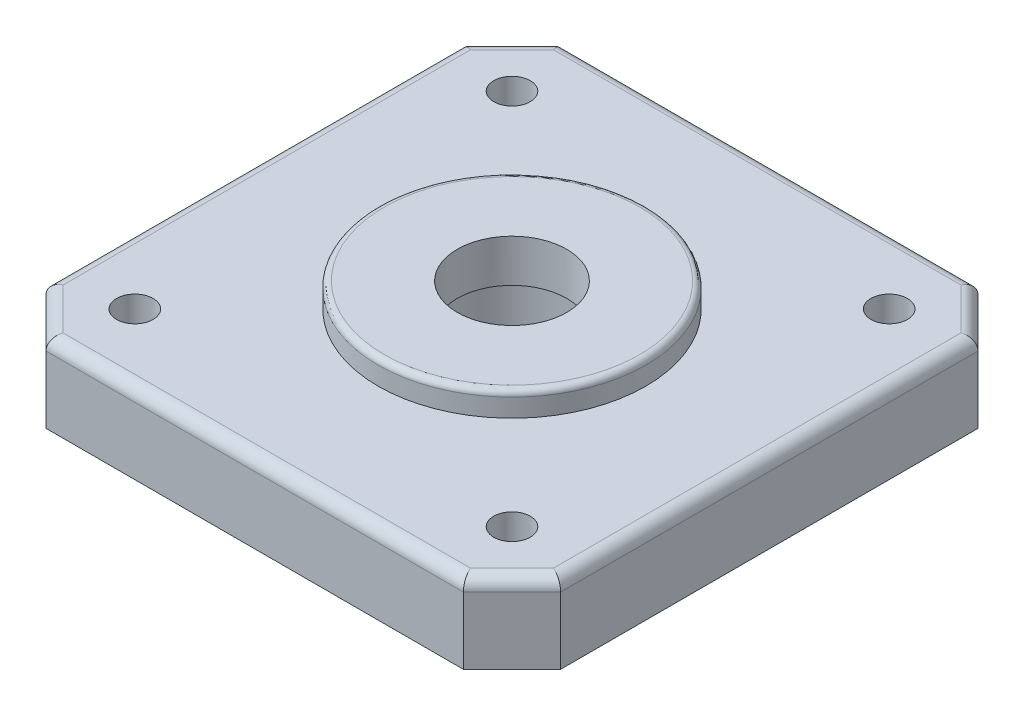
SolidWorks part; units mm, degrees
ref_plane "Front Plane" through (0, 0, 0) normal (0, 0, 1) x (1, 0, 0)
ref_plane "Top Plane" through (0, 0, 0) normal (0, 1, 0) x (1, 0, 0)
ref_plane "Right Plane" through (0, 0, 0) normal (1, 0, 0) x (0, 0, -1)
sketch "Sketch1" plane through (0, 0, 0) normal (0, 1, 0) x (1, 0, 0)
  line L0 (-21.15, 17.15) -> (-17.15, 21.15)
  line L1 (-17.15, 21.15) -> (17.15, 21.15)
  line L2 (-21.15, 17.15) -> (-21.15, -17.15)
  line L3 (-17.15, -21.15) -> (17.15, -21.15)
  line L4 (21.15, 17.15) -> (21.15, -17.15)
  line L5 (-21.15, 21.15) -> (21.15, -21.15) construction
  line L6 (-21.15, -21.15) -> (21.15, 21.15) construction
  line L7 (-21.15, -17.15) -> (-17.15, -21.15)
  line L8 (17.15, -21.15) -> (21.15, -17.15)
  line L9 (17.15, 21.15) -> (21.15, 17.15)
  point P0 (0, 0)
  dimension "D1" = 42.3
  dimension "D2" = 42.3
extrude "Boss-Extrude1" add sketch "Sketch1" along normal blind 6.5
sketch "Sketch2" plane through (0, 6.5, 0) normal (0, 1, 0) x (1, 0, 0)
  circle A0 centre (0, 0) radius 11
  dimension "D1" = 22
extrude "Boss-Extrude2" add sketch "Sketch2" along normal blind 2
sketch "Sketch3" plane through (0, 6.5, 0) normal (0, 1, 0) x (1, 0, 0)
  line L1 (-15.5, 15.5) -> (15.5, 15.5) construction
  line L2 (-15.5, 15.5) -> (-15.5, -15.5) construction
  line L3 (-15.5, -15.5) -> (15.5, -15.5) construction
  line L4 (15.5, 15.5) -> (15.5, -15.5) construction
  line L5 (-15.5, 15.5) -> (15.5, -15.5) construction
  line L6 (-15.5, -15.5) -> (15.5, 15.5) construction
  circle A0 centre (-15.5, 15.5) radius 1.5
  circle A1 centre (15.5, 15.5) radius 1.5
  circle A2 centre (-15.5, -15.5) radius 1.5
  circle A3 centre (15.5, -15.5) radius 1.5
  point P0 (0, 0)
  dimension "D3" = 3
  dimension "D1" = 31
  dimension "D2" = 31
extrude "Cut-Extrude2" cut sketch "Sketch3" against normal blind 6.5
sketch "Sketch4" plane through (0, 8.5, 0) normal (0, 1, 0) x (1, 0, 0)
  circle A0 centre (0, 0) radius 4.5
  dimension "D1" = 9
extrude "Cut-Extrude3" cut sketch "Sketch4" against normal blind 8.5
sketch "Sketch5" plane through (0, 0, 0) normal (0, -1, 0) x (1, 0, 0)
  circle A0 centre (0, 0) radius 5.5
  dimension "D1" = 11
extrude "Cut-Extrude4" cut sketch "Sketch5" against normal blind 5
fillet "Fillet1" radius 1 8 edges at (19.15, 6.5, -19.15) (21.15, 6.5, 0) (19.15, 6.5, 19.15) (0, 6.5, 21.15) (-19.15, 6.5, 19.15) (-21.15, 6.5, 0) (-19.15, 6.5, -19.15) (0, 6.5, -21.15)
fillet "Fillet2" radius 0.5 1 edges at (0, 8.5, 11)
